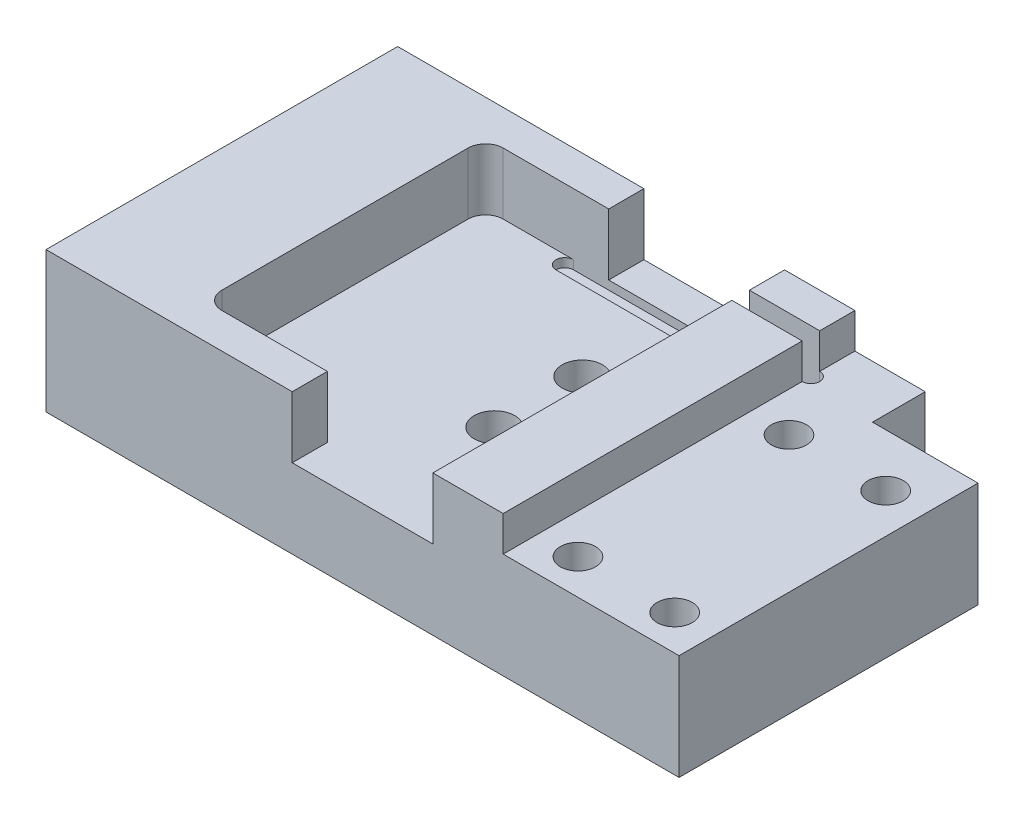
SolidWorks part; units mm, degrees
other "标注1"
sketch "草图12" plane through (-36, 0, -20) normal (0, 0, -1) x (-1, 0, 0)
ref_plane "前视基准面" through (0, 0, 0) normal (0, 0, 1) x (1, 0, 0)
ref_plane "上视基准面" through (0, 0, 0) normal (0, 1, 0) x (1, 0, 0)
ref_plane "右视基准面" through (0, 0, 0) normal (1, 0, 0) x (0, 0, -1)
sketch "草图1" plane through (0, 0, 0) normal (0, 1, 0) x (1, 0, 0)
  line L1 (0, 0) -> (-36, 0)
  line L2 (0, 0) -> (0, 20)
  line L3 (0, 20) -> (-36, 20)
  line L4 (-36, 0) -> (-36, 20)
  dimension "D1" = 36
  dimension "D2" = 20
extrude "凸台-拉伸1" add sketch "草图1" along normal blind 8
sketch "草图2" plane through (0, 8, 0) normal (0, 1, 0) x (1, 0, 0)
  line L0 (0, 20) -> (-36, 20) construction
  line L1 (-14, 20) -> (-22, 20)
  line L2 (-14, 20) -> (-14, 0)
  line L3 (-14, 0) -> (-22, 0)
  line L4 (-22, 20) -> (-22, 0)
  line L5 (-36, 0) -> (0, 0) construction
  line L6 (0, 10) -> (-14, 10) construction
  line L7 (0, 0) -> (0, 20) construction
  line L8 (-22, 10) -> (-36, 10) construction
  line L9 (-36, 20) -> (-36, 0) construction
  dimension "D1" = 8
extrude "切除-拉伸1" cut sketch "草图2" against normal blind 3.5
sketch "草图3" plane through (0, 0, 0) normal (0, -1, 0) x (-1, 0, 0)
  line L0 (0, 10) -> (8, 10) construction
  line L3 (0, 0) -> (0, 20) construction
  line L4 (28, 10) -> (36, 10) construction
  line L5 (36, 20) -> (36, 0) construction
  circle A2 centre (8, 10) radius 2.5
  circle A3 centre (28, 10) radius 2.5
  dimension "D1" = 5
  dimension "D2" = 20
extrude "切除-拉伸2" cut sketch "草图3" against normal blind 4
sketch "草图5" plane through (0, 8, 0) normal (0, 1, 0) x (1, 0, 0)
  line L0 (-22, 20) -> (-22, 0) construction
  line L1 (-22, 18) -> (-29, 18)
  line L2 (-22, 18) -> (-22, 2)
  line L3 (-22, 2) -> (-29, 2)
  line L4 (-29, 18) -> (-29, 2)
  line L5 (-25.5, 18) -> (-25.5, 20) construction
  line L6 (-22, 20) -> (-36, 20) construction
  line L7 (-25.5, 2) -> (-25.5, 0) construction
  line L8 (-36, 0) -> (-22, 0) construction
  dimension "D1" = 16
  dimension "D2" = 7
extrude "切除-拉伸4" cut sketch "草图5" against normal blind 3.5
fillet "圆角1" radius 1 2 edges at (-29, 6.25, -2) (-29, 6.25, -18)
sketch "草图6" plane through (0, 4.5, 0) normal (0, 1, 0) x (1, 0, 0)
  line L0 (-18, 20) -> (-18, 12.5) construction
  line L1 (-18, 7.5) -> (-18, 0) construction
  line L2 (-22, 0) -> (-14, 0) construction
  line L3 (-14, 20) -> (-22, 20) construction
  circle A0 centre (-18, 12.5) radius 1.15
  circle A1 centre (-18, 7.5) radius 1.15
  dimension "D2" = 2.3
  dimension "D1" = 5
extrude "切除-拉伸5" cut sketch "草图6" against normal through all
sketch "草图7" plane through (0, 8, 0) normal (0, 1, 0) x (1, 0, 0)
  line L0 (-14, 0) -> (0, 0) construction
  line L1 (0, 20) -> (-10, 20)
  line L2 (0, 20) -> (0, 0)
  line L3 (0, 0) -> (-10, 0)
  line L4 (-10, 20) -> (-10, 0)
  dimension "D1" = 10
extrude "切除-拉伸6" cut sketch "草图7" against normal blind 2
sketch "草图8" plane through (0, 8, 0) normal (0, 1, 0) x (1, 0, 0)
  line L0 (-22, 18) -> (-28, 18) construction
  line L1 (-24, 18) -> (-10, 18)
  line L3 (-24, 17) -> (-10, 17)
  line L5 (-10, 20) -> (-10, 0) construction
  arc A0 (-10, 17) -> (-10, 18) centre (-10, 17.5) ccw
  arc A1 (-24, 18) -> (-24, 17) centre (-24, 17.5) ccw
  dimension "D1" = 1
extrude "切除-拉伸7" cut sketch "草图8" against normal blind 4
sketch "草图9" plane through (0, 6, 0) normal (0, 1, 0) x (1, 0, 0)
  line L0 (-2.25, 2) -> (-7.75, 2) construction
  line L1 (-7.75, 2) -> (-7.75, 14) construction
  line L2 (-7.75, 14) -> (-2.25, 14) construction
  line L3 (-2.25, 14) -> (-2.25, 2) construction
  line L6 (-2.25, 2) -> (-2.25, 0) construction
  line L7 (-10, 0) -> (0, 0) construction
  line L8 (-2.25, 2) -> (0, 2) construction
  line L9 (0, 0) -> (0, 20) construction
  line L10 (-7.75, 2) -> (-10, 2) construction
  line L11 (-10, 17) -> (-10, 0) construction
  circle A0 centre (-2.25, 2) radius 1
  circle A1 centre (-7.75, 2) radius 1
  circle A2 centre (-2.25, 14) radius 1
  circle A3 centre (-7.75, 14) radius 1
  dimension "D1" = 2
  dimension "D2" = 5.5
  dimension "D3" = 12
  dimension "D4" = 2
extrude "切除-拉伸10" cut sketch "草图9" against normal blind 3
sketch "草图10" plane through (0, 0, 0) normal (0, -1, 0) x (-1, 0, 0)
  circle A0 centre (18, 12.5) radius 2
  circle A1 centre (18, 7.5) radius 2
  dimension "D1" = 4
  dimension "D2" = 4
extrude "切除-拉伸11" cut sketch "草图10" against normal blind 2.4
sketch "草图11" plane through (0, 0, -20) normal (0, 0, -1) x (-1, 0, 0)
  line L0 (0, 3) -> (3, 3) construction
  line L1 (0, 6) -> (0, 0) construction
  line L2 (33, 3) -> (36, 3) construction
  line L3 (36, 8) -> (36, 0) construction
  line L4 (0, 0) -> (36, 0) construction
  line L10 (0, 0) -> (6, 0)
  line L11 (0, 0) -> (0, 6)
  line L12 (0, 6) -> (6, 6)
  line L13 (6, 0) -> (6, 6)
  line L14 (36, 0) -> (30, 0)
  line L15 (36, 0) -> (36, 6)
  line L16 (36, 6) -> (30, 6)
  line L17 (30, 0) -> (30, 6)
  circle A0 centre (3, 3) radius 2.85 construction
  circle A1 centre (33, 3) radius 2.85 construction
  dimension "D2" = 5.7
  dimension "D1" = 3
  dimension "D3" = 30
  dimension "D4" = 6
extrude "切除-拉伸15" cut sketch "草图11" against normal blind 3
